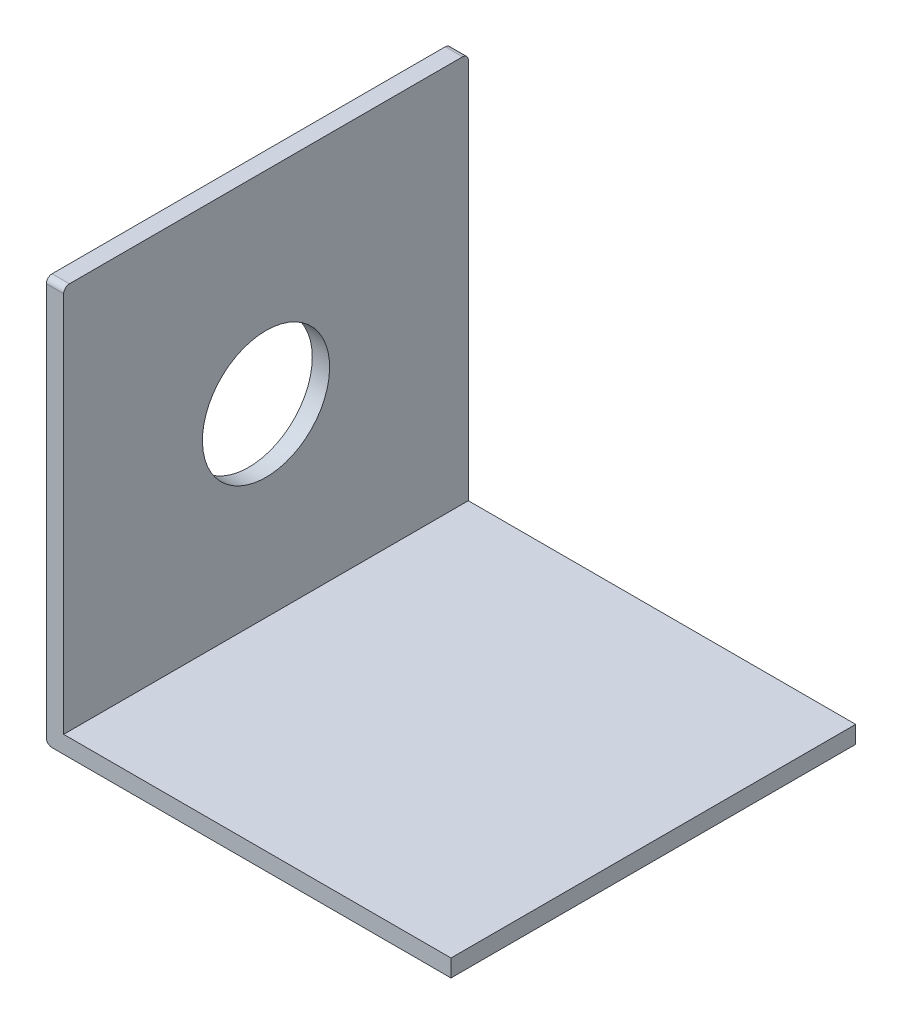
SolidWorks part; units mm, degrees
ref_plane "Plan de face" through (0, 0, 0) normal (0, 0, 1) x (1, 0, 0)
ref_plane "Plan de dessus" through (0, 0, 0) normal (0, 1, 0) x (1, 0, 0)
ref_plane "Plan de droite" through (0, 0, 0) normal (1, 0, 0) x (0, 0, -1)
sketch "Esquisse1" plane through (0, 0, 0) normal (0, 0, 1) x (1, 0, 0)
  line L0 (0, 0) -> (70, 0)
  line L1 (0, 0) -> (0, 70)
  line L2 (0, 70) -> (3, 70)
  line L3 (3, 70) -> (3, 3)
  line L4 (3, 3) -> (70, 3)
  line L5 (70, 3) -> (70, 0)
  dimension "D1" = 3
  dimension "D2" = 3
  dimension "D3" = 70
  dimension "D4" = 70
extrude "Boss.-Extru.1" add sketch "Esquisse1" along normal blind 70
sketch "Esquisse2" plane through (3, 0, 0) normal (1, 0, 0) x (0, 0, -1)
  line L0 (0, 3) -> (0, 70) construction
  line L1 (-70, 70) -> (0, 70) construction
  circle A0 centre (-35, 35) radius 11
  dimension "D1" = 22
  dimension "D2" = 35
  dimension "D3" = 35
extrude "Enlèv. mat.-Extru.1" cut sketch "Esquisse2" against normal blind 70
fillet "Congé8" radius 1 1 edges at (0, 0, 35)
fillet "Congé9" radius 1 2 edges at (1.5, 70, 70) (1.5, 70, 0)
